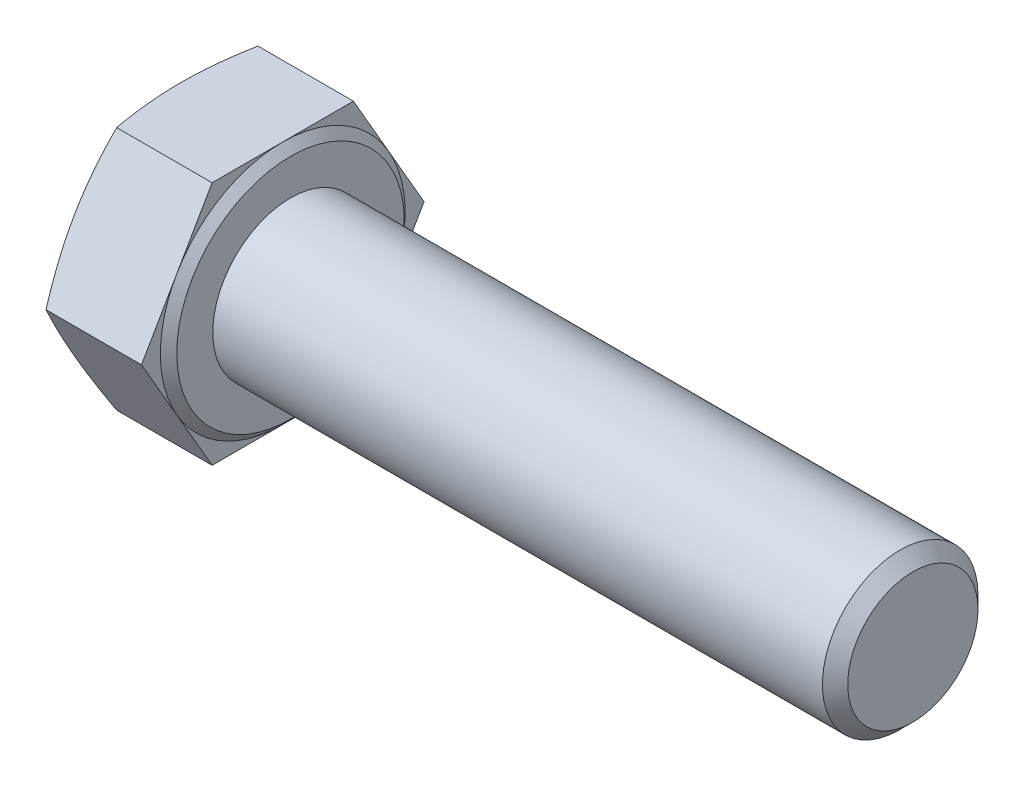
SolidWorks part; units mm, degrees
ref_plane "Front" through (0, 0, 0) normal (0, 0, 1) x (1, 0, 0)
ref_plane "Top" through (0, 0, 0) normal (0, 1, 0) x (1, 0, 0)
ref_plane "Right" through (0, 0, 0) normal (1, 0, 0) x (0, 0, -1)
sketch "Sketch-BaseHead" plane through (0, 0, 0) normal (1, 0, 0) x (0, 0, -1)
  line L1 (9.0817, 0) -> (4.5409, 7.865)
  line L2 (4.5409, 7.865) -> (-4.5409, 7.865)
  line L3 (-4.5409, 7.865) -> (-9.0817, 0)
  line L4 (-9.0817, 0) -> (-4.5409, -7.865)
  line L5 (-4.5409, -7.865) -> (4.5409, -7.865)
  line L6 (4.5409, -7.865) -> (9.0817, 0)
  circle A0 centre (0, 0) radius 7.865 construction
  dimension "s" = 15.73
extrude "BaseHead" add sketch "Sketch-BaseHead" along normal blind 6.58
sketch "Sketch4" plane through (-0.2646, 0, 5.9169) normal (0, 1, 0) x (0, 0, -1)
  line L0 (5.9169, 3.7369) -> (5.9169, -10.4477) construction
  line L2 (14.9986, -0.2646) -> (13.7819, -0.2646)
  line L4 (13.7819, -0.2646) -> (14.9986, -0.7075)
  line L6 (14.9986, -0.7075) -> (14.9986, -0.2646)
  dimension "D1" = 20
  dimension "D2" = 15.73
revolve "HeadChamfer" cut sketch "Sketch4" angle 360 about L0
sketch "Sketch1" plane through (0, 0, 0) normal (0, 0, 1) x (1, 0, 0)
  line L0 (6.58, 0) -> (7.08, 0)
  line L1 (7.08, 0) -> (7.08, -7.315)
  line L2 (7.08, -7.315) -> (6.58, -7.865)
  line L3 (6.58, -7.865) -> (6.58, 0) construction
  line L4 (0, 0) -> (7.5821, 0) construction
  line L5 (-4.0016, 0) -> (10.1831, 0) construction
  line L6 (6.58, -7.865) -> (0.4428, -7.865) construction
  line L7 (6.58, 0) -> (6.58, -7.865)
  dimension "c" = 0.5
  dimension "D1" = 7.865
  dimension "D2" = 7.315
revolve "Revolve1" add sketch "Sketch1" angle 360 about axis through (-4.0016, 0, 0) along (1, 0, 0)
ref_plane "Plane2" through (31.08, 0, 0) normal (1, 0, 0) x (0, 0, -1)
sketch "Sketch3" plane through (7.08, 0, 0) normal (1, 0, 0) x (0, 0, -1)
  circle A0 centre (0, 0) radius 5
  dimension "d" = 10
extrude "BaseBody" add sketch "Sketch3" along normal blind 40
cosmetic thread "ThreadCosmetic1" [suppressed] parameters "b"=16, "D2"=8.376
fillet "HeadFillet" [suppressed] radius 0.4
chamfer "Chamfer1" distance 0.812 angle 45 1 edges at (47.08, 0, -5)
sketch "Sketch5" plane through (0, 0, 0) normal (0, 0, 1) x (1, 0, 0)
  line L0 (45.456, 5.812) -> (46.268, 5.812)
  line L1 (46.268, 5.812) -> (46.268, 5)
  line L2 (46.268, 5) -> (45.862, 4.2968)
  line L3 (45.862, 4.2968) -> (45.456, 5)
  line L4 (45.456, 5) -> (45.456, 5.812)
  line L5 (46.268, -5) -> (46.268, 5) construction
  line L6 (46.268, 5) -> (7.08, 5) construction
  dimension "D1" = 0.812
revolve "Cut-Revolve10" [suppressed] cut sketch "Sketch5" angle 360
pattern_linear "LPattern10" [suppressed] count 16
equation "\"D1@Sketch1\" = \"s@Sketch-BaseHead\"/ 2"
equation "\"D2@Sketch4\" = \"s@Sketch-BaseHead\""
equation "\"D1@Chamfer1\" =  ( \"d@Sketch3\" - \"D2@ThreadCosmetic1\" ) / 2 "
equation "\"b@ThreadCosmetic1\" = \"l@BaseBody\" - \"lg@Plane2\""
equation "\"D1@Sketch5\" =  (\"d@Sketch3\" - \"D2@ThreadCosmetic1\" )  / 2 "
equation "\"pitch@LPattern10\" = 1.2 * \"D1@Sketch5\""
equation "\"D1@LPattern10\" = \"b@ThreadCosmetic1\" / \"pitch@LPattern10\""
